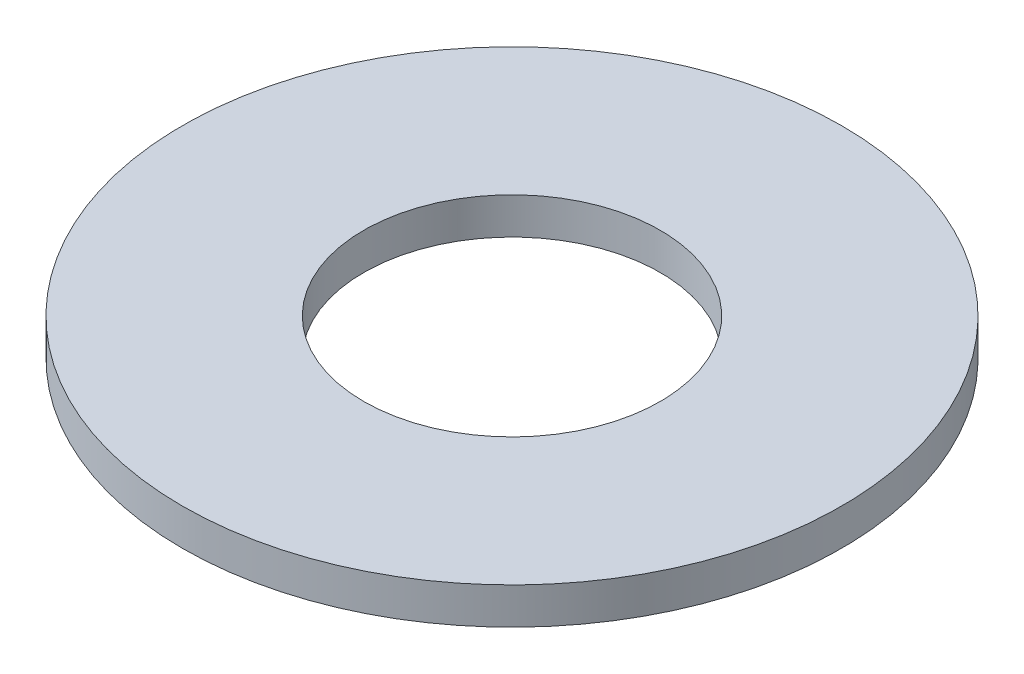
SolidWorks part; units mm, degrees
ref_plane "Front Plane" through (0, 0, 0) normal (0, 0, 1) x (1, 0, 0)
ref_plane "Top Plane" through (0, 0, 0) normal (0, 1, 0) x (1, 0, 0)
ref_plane "Right Plane" through (0, 0, 0) normal (1, 0, 0) x (0, 0, -1)
sketch "Sketch1" plane through (0, 0, 0) normal (0, 1, 0) x (1, 0, 0)
  circle A0 centre (0, 0) radius 4.05
  circle A1 centre (0, 0) radius 9
  dimension "D1" = 8.1
  dimension "D2" = 18
extrude "Boss-Extrude1" add sketch "Sketch1" along normal blind 1
